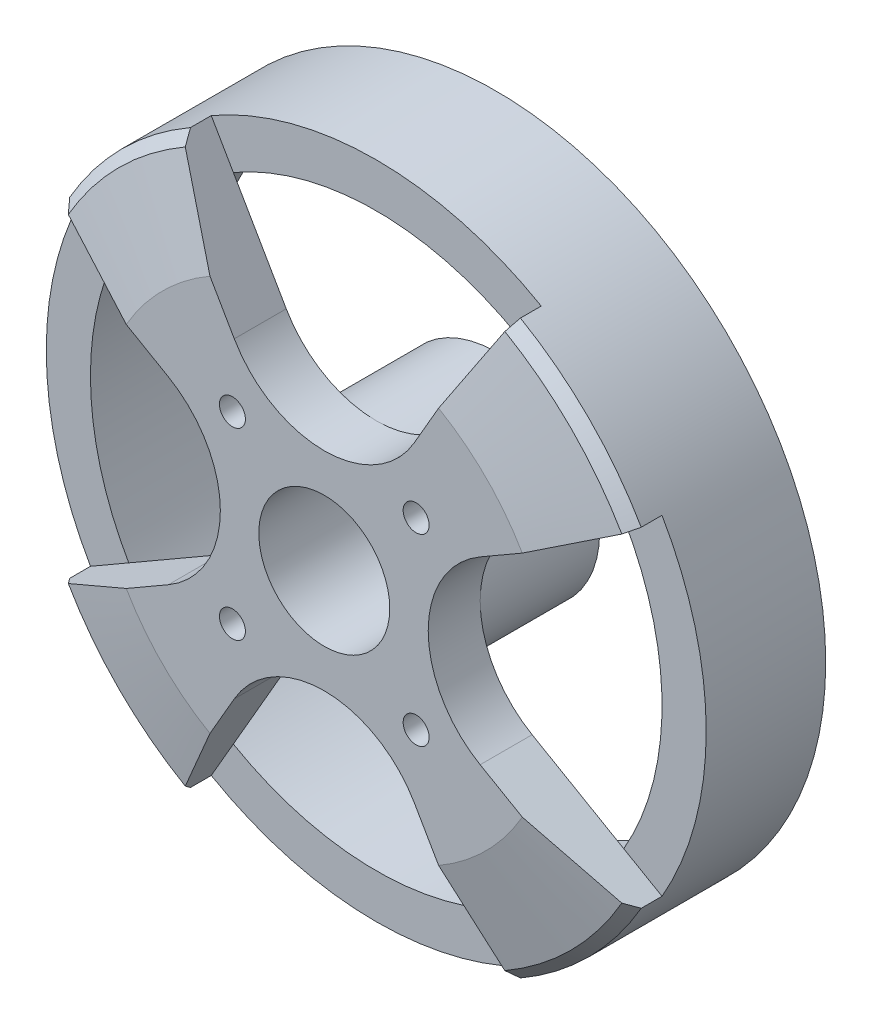
SolidWorks part; units mm, degrees
material "Сплав 2024"
ref_plane "Спереди" through (0, 0, 0) normal (0, 0, 1) x (1, 0, 0)
ref_plane "Сверху" through (0, 0, 0) normal (0, 1, 0) x (1, 0, 0)
ref_plane "Справа" through (0, 0, 0) normal (1, 0, 0) x (0, 0, -1)
sketch "Эскиз1" plane through (0, 0, 0) normal (0, 0, 1) x (1, 0, 0)
  circle A0 centre (0, 0) radius 31.75
  dimension "D1" = 63.5
extrude "Бобышка-Вытянуть1" add sketch "Эскиз1" along normal blind 14.5
chamfer "Фаска1" distance 1 angle 45 1 edges at (31.75, 0, 14.5)
ref_plane "Плоскость1" through (0, 0, 16.5) normal (0, 0, 1) x (1, 0, 0)
sketch "Эскиз2" plane through (0, 0, 16.5) normal (0, 0, 1) x (1, 0, 0)
  circle A0 centre (0, 0) radius 22
  dimension "D1" = 44
sketch "Эскиз3" plane through (0, 0, 14.5) normal (0, 0, 1) x (1, 0, 0)
  circle A0 centre (0, 0) radius 30.75
  dimension "D1" = 61.5
loft "По сечениям3" add profiles "Эскиз3", "Эскиз2"
sketch "Эскиз4" plane through (0, 0, 16.5) normal (0, 0, 1) x (1, 0, 0)
  line L0 (0, 31.75) -> (0, -31.75) construction
  line L1 (-31.75, 0) -> (31.75, 0) construction
  circle A0 centre (0, 0) radius 31.75 construction
  circle A1 centre (0, 0) radius 6.3
  dimension "D1" = 12.6
extrude "Вырез-Вытянуть1" cut sketch "Эскиз4" against normal through all
sketch "Эскиз5" plane through (0, 0, 16.5) normal (0, 0, 1) x (1, 0, 0)
  line L0 (0, 31.75) -> (0, -31.75) construction
  line L1 (31.75, 0) -> (-31.75, 0) construction
  line L2 (-8.6603, 15) -> (-15.875, 27.4963)
  line L3 (15.875, 27.4963) -> (8.6603, 15)
  line L4 (15, 8.6603) -> (27.4963, 15.875)
  line L5 (27.4963, -15.875) -> (15, -8.6603)
  line L6 (8.6603, -15) -> (15.875, -27.4963)
  line L7 (-15.875, -27.4963) -> (-8.6603, -15)
  line L8 (-15, -8.6603) -> (-27.4963, -15.875)
  line L9 (-27.4963, 15.875) -> (-15, 8.6603)
  circle A0 centre (0, 0) radius 31.75 construction
  arc A1 (-8.6603, 15) -> (8.6603, 15) centre (0, 20) ccw
  arc A2 (27.4963, 15.875) -> (27.4963, -15.875) centre (0, 0) cw
  arc A3 (15, 8.6603) -> (15, -8.6603) centre (20, 0) ccw
  arc A4 (15.875, -27.4963) -> (-15.875, -27.4963) centre (0, 0) cw
  circle A5 centre (0, 0) radius 20 construction
  arc A6 (-15.875, 27.4963) -> (15.875, 27.4963) centre (0, 0) cw
  arc A7 (8.6603, -15) -> (-8.6603, -15) centre (0, -20) ccw
  arc A8 (-27.4963, -15.875) -> (-27.4963, 15.875) centre (0, 0) cw
  arc A9 (-15, -8.6603) -> (-15, 8.6603) centre (-20, 0) ccw
  point P33 (0, 0)
  dimension "D1" = 20
  dimension "D2" = 4
  dimension "D5" = 40
  dimension "D6" = 60
  dimension "D7" = 30
extrude "Вырез-Вытянуть2" cut sketch "Эскиз5" against normal blind 5
sketch "Эскиз6" plane through (0, 0, 0) normal (0, 0, -1) x (-1, 0, 0)
  circle A0 centre (0, 0) radius 27.5
  dimension "D1" = 55
extrude "Вырез-Вытянуть3" cut sketch "Эскиз6" against normal up to surface (11.5 mm away) up to face at (0, 21.0616, 11.5)
sketch "Эскиз7" plane through (0, 0, 16.5) normal (0, 0, 1) x (1, 0, 0)
  line L0 (-15.5563, 15.5563) -> (15.5563, -15.5563) construction
  line L1 (15.5563, 15.5563) -> (-15.5563, -15.5563) construction
  arc A0 (-11, 19.0526) -> (-19.0526, 11) centre (0, 0) ccw construction
  arc A1 (11, -19.0526) -> (19.0526, -11) centre (0, 0) ccw construction
  arc A2 (19.0526, 11) -> (11, 19.0526) centre (0, 0) ccw construction
  arc A3 (-19.0526, -11) -> (-11, -19.0526) centre (0, 0) ccw construction
  circle A4 centre (0, 0) radius 12.5 construction
  dimension "D1" = 25
hole_wizard "Отверстие обработанное метчиком M3x0.51" positions "Эскиз9" profile "Эскиз10" tap size "M3x0.5" standard "Ansi Metric" end condition through all
sketch "Эскиз9" plane through (0, 0, 16.5) normal (0, 0, 1) x (1, 0, 0)
  line L0 (-15.5563, 15.5563) -> (15.5563, -15.5563) construction
  line L1 (15.5563, 15.5563) -> (-15.5563, -15.5563) construction
  circle A0 centre (0, 0) radius 12.5 construction
  point P0 (-8.8388, 8.8388)
  point P6 (-8.8388, -8.8388)
  point P10 (8.8388, -8.8388)
  point P12 (8.8388, 8.8388)
sketch "Эскиз10" plane through (-8.8388, 8.8388, 16.5) normal (1, 0, 0) x (0, -1, 0)
  line L0 (0, 0) -> (0, 16.5)
  line L1 (0, 16.5) -> (1.25, 16.5)
  line L2 (1.25, 16.5) -> (1.25, 0)
  line L5 (1.25, 0) -> (0, 0)
  line L11 (0, -6.35) -> (0, 107.95) construction
  dimension "Диаметр проходного сверла" = 2.5
  dimension "Глубина проходного сверла" = 16.5
cosmetic thread "Отверстие резьбы1" parameters "D2"=3
cosmetic thread "Отверстие резьбы2" parameters "D2"=3
cosmetic thread "Отверстие резьбы3" parameters "D2"=3
cosmetic thread "Отверстие резьбы4" parameters "D2"=3
sketch "Эскиз11" plane through (0, 0, 11.5) normal (0, 0, -1) x (-1, 0, 0)
  circle A0 centre (0, 0) radius 6.3
  circle A1 centre (0, 0) radius 10
  dimension "D1" = 12.6
  dimension "D2" = 20
extrude "Бобышка-Вытянуть2" add sketch "Эскиз11" along normal up to surface (11.5 mm away) up to face at (-27.5, 0, 0)
